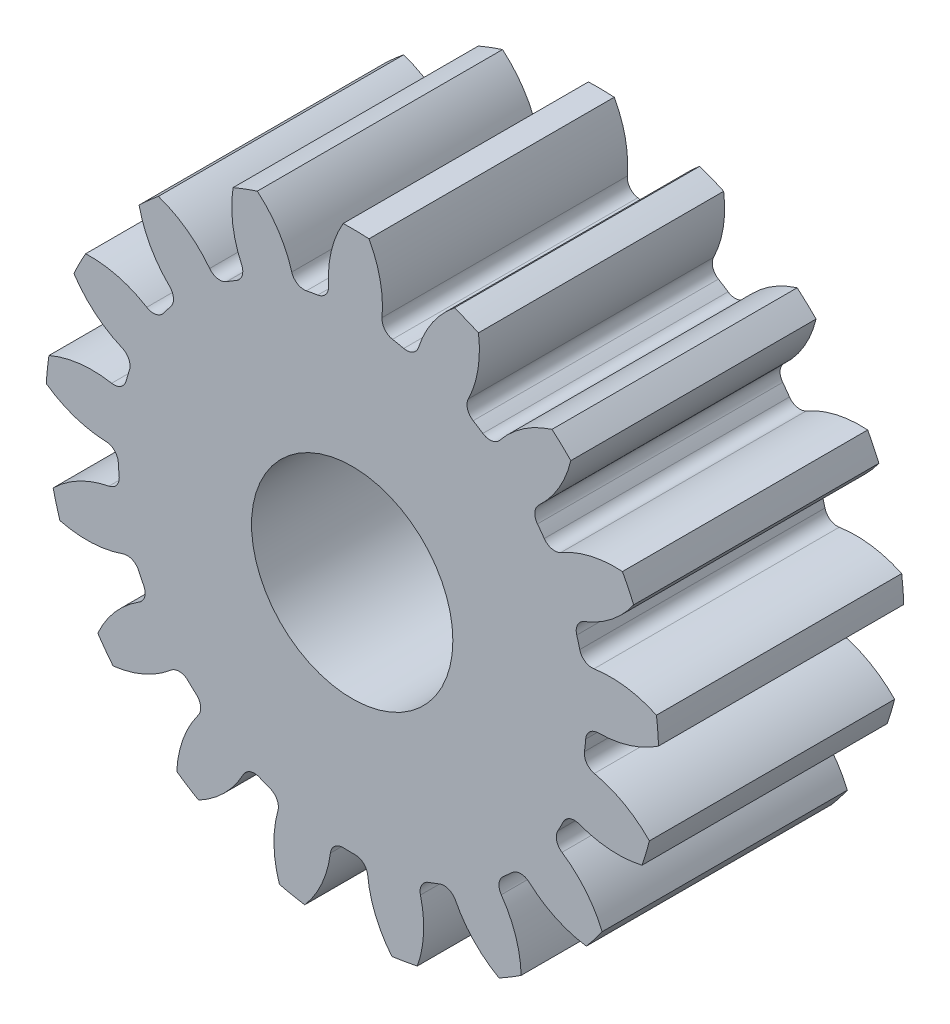
SolidWorks part; units mm, degrees
ref_plane "Front" through (0, 0, 0) normal (0, 0, 1) x (1, 0, 0)
ref_plane "Top" through (0, 0, 0) normal (0, 1, 0) x (1, 0, 0)
ref_plane "Right" through (0, 0, 0) normal (1, 0, 0) x (0, 0, -1)
sketch "Sketch3" plane through (0, 0, 0) normal (0, 0, 1) x (1, 0, 0)
  circle A0 centre (0, 0) radius 12.065
  dimension "od" = 24.13
extrude "gearBody" add sketch "Sketch3" along normal blind 9.652
sketch "Sketch2" plane through (0, 0, 0) normal (0, 0, 1) x (1, 0, 0)
  line L0 (0, 0) -> (9.6556, 3.9995) construction
  line L1 (12.5726, -4.3051) -> (0, 0) construction
  line L2 (0, 0) -> (36.3143, 0) construction
  line L3 (10.7942, -0.1298) -> (10.5835, -2.1262) construction
  line L5 (10.6889, -1.128) -> (0, 0) construction
  line L7 (0, 0) -> (10.4512, 0) construction
  arc A0 (10.449, -0.2097) -> (10.2627, -1.9759) centre (0, 0) ccw construction
  arc A1 (12.0565, 0.4523) -> (11.6965, -2.9589) centre (0, 0) ccw construction
  arc A2 (10.7942, -0.1298) -> (10.5835, -2.1262) centre (0, 0) ccw construction
  arc A3 (9.1428, -1.192) -> (9.1902, -0.7427) centre (0, 0) ccw
  arc A4 (12.5726, -4.3051) -> (9.5303, -1.7439) centre (8.6081, -5.9268) ccw
  arc A5 (12.5726, -4.3051) -> (13.1942, 1.5859) centre (0, 0) ccw
  arc A6 (13.1942, 1.5859) -> (9.6844, -0.2838) centre (9.6556, 3.9995) cw
  arc A7 (9.1902, -0.7427) -> (9.6844, -0.2838) centre (9.6877, -0.7829) cw
  arc A8 (9.5303, -1.7439) -> (9.1428, -1.192) centre (9.6377, -1.2565) cw
  point P6 (13.1942, 1.5859)
  point P22 (12.5726, -4.3051)
  dimension "baseDia" = 20.9023
  dimension "od" = 24.13
  dimension "pd" = 21.59
  dimension "rd" = 18.4404
  dimension "rFillet" = 0.4991
  dimension "pointX" = 13.1942
  dimension "pointY" = 1.5859
  dimension "CTT" = 1.9964
  dimension "flankCenterAngle" = 22.5
extrude "toothCut" cut sketch "Sketch2" along normal through all
pattern_circular "CirPattern1" count 17 over 360 about axis through (0, 0, 0) along (0, 0, 1) of "toothCut"
sketch "hub1Dia" plane through (0, 0, 0) normal (0, 0, -1) x (-1, 0, 0)
  circle A0 centre (0, 0) radius 25.4
  dimension "hub1Dia" = 50.8
extrude "hub1" [suppressed] add sketch "hub1Dia" along normal blind 19.05
sketch "hub2Dia" plane through (0, 0, 9.652) normal (0, 0, 1) x (1, 0, 0)
  circle A0 centre (0, 0) radius 21.844
  dimension "hub2dia" = 43.688
extrude "hub2" [suppressed] add sketch "hub2Dia" along normal blind 16.002
sketch "boreDia" plane through (0, 0, 0) normal (0, 0, 1) x (1, 0, 0)
  circle A0 centre (0, 0) radius 3.9624
  dimension "boreDia" = 7.9248
extrude "bore" cut sketch "boreDia" against normal mid plane 25400
chamfer "hub2Chamfer" [suppressed] distance 0.508 angle 45
chamfer "hub2BoreChamfer" [suppressed] distance 0.508 angle 45
chamfer "hub1BoreChamfer" [suppressed] distance 0.508 angle 45
chamfer "hub1Chamfer" [suppressed] distance 0.508 angle 45
chamfer "BoreChamfer2" [suppressed] distance 0.508 angle 45
chamfer "boreChamfer1" [suppressed] distance 0.508 angle 45
